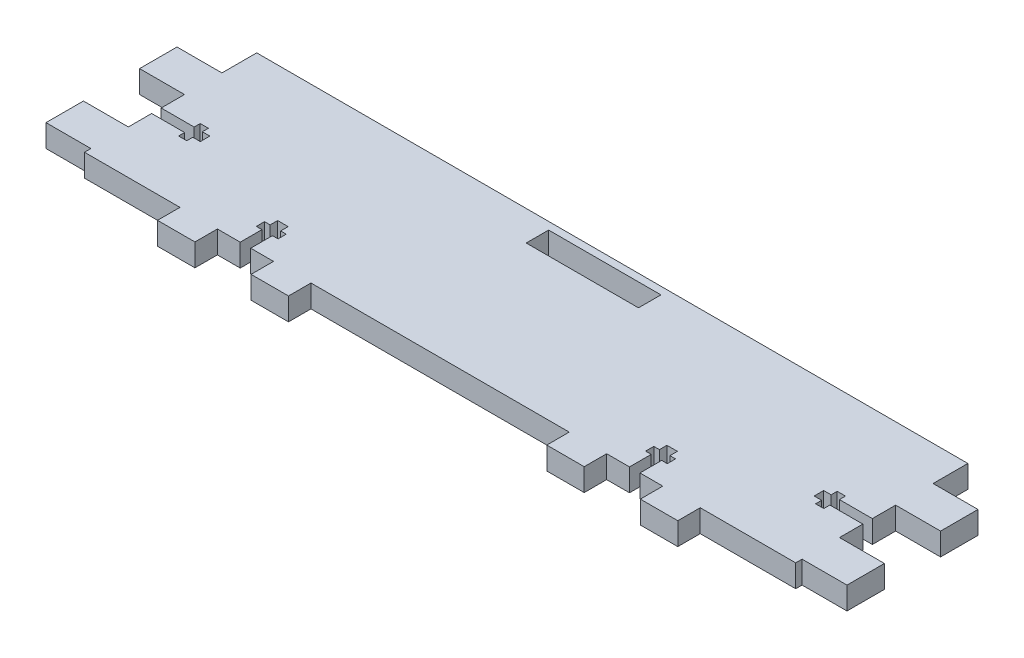
SolidWorks part; units mm, degrees
ref_plane "Front" through (0, 0, 0) normal (0, 0, 1) x (1, 0, 0)
ref_plane "Top" through (0, 0, 0) normal (0, 1, 0) x (1, 0, 0)
ref_plane "Right" through (0, 0, 0) normal (1, 0, 0) x (0, 0, -1)
sketch "Эскиз1" plane through (0, 0, 0) normal (0, 1, 0) x (1, 0, 0)
  line L0 (-131.8881, 0) -> (137.6783, 0) construction
  line L1 (-95, 23) -> (95, 23)
  line L2 (-95, 23) -> (-95, 13.7093)
  line L3 (-95, -23) -> (-69.5, -23)
  line L4 (95, 23) -> (95, 13.7093)
  line L5 (-95, 23) -> (95, -23) construction
  line L6 (-95, -23) -> (95, 23) construction
  line L7 (0, 62.5664) -> (0, -52.5944) construction
  line L8 (69.5, 51.8234) -> (69.5, -44.3584) construction
  line L9 (59.5, 51.8234) -> (59.5, -44.3584) construction
  line L10 (34.5, 51.8234) -> (34.5, -44.3584) construction
  line L11 (44.5, 51.8234) -> (44.5, -44.3584) construction
  line L12 (106.5886, -29) -> (-1.3442, -29) construction
  line L13 (59.5, -23) -> (59.5, -29)
  line L14 (59.5, -29) -> (69.5, -29)
  line L15 (69.5, -29) -> (69.5, -23)
  line L16 (34.5, -23) -> (34.5, -29)
  line L17 (34.5, -29) -> (44.5, -29)
  line L18 (44.5, -29) -> (44.5, -23)
  line L19 (52, -9.9523) -> (52, -35.233) construction
  line L20 (44.5, -23) -> (50.6, -23)
  line L21 (69.5, -23) -> (95, -23)
  line L22 (102.7865, -17.2) -> (39.4134, -17.2) construction
  line L23 (103.2055, -15) -> (39.8324, -15) construction
  line L24 (103.3102, -13) -> (39.9371, -13) construction
  line L25 (50.6, -27.2711) -> (50.6, -9.9523) construction
  line L26 (49.1, -27.2711) -> (49.1, -9.9523) construction
  line L27 (50.6, -23) -> (50.6, -17.2)
  line L28 (50.6, -17.2) -> (49.1, -17.2)
  line L29 (49.1, -17.2) -> (49.1, -15)
  line L30 (49.1, -15) -> (50.6, -15)
  line L31 (50.6, -15) -> (50.6, -13)
  line L32 (50.6, -13) -> (53.4, -13)
  line L33 (53.4, -23) -> (53.4, -17.2)
  line L34 (53.4, -17.2) -> (54.9, -17.2)
  line L35 (54.9, -17.2) -> (54.9, -15)
  line L36 (54.9, -15) -> (53.4, -15)
  line L37 (53.4, -15) -> (53.4, -13)
  line L38 (53.4, -23) -> (59.5, -23)
  line L39 (-50.6, -17.2) -> (-49.1, -17.2)
  line L40 (-49.1, -17.2) -> (-49.1, -15)
  line L41 (-49.1, -15) -> (-50.6, -15)
  line L42 (-50.6, -15) -> (-50.6, -13)
  line L43 (-50.6, -13) -> (-53.4, -13)
  line L44 (-53.4, -15) -> (-53.4, -13)
  line L45 (-54.9, -15) -> (-53.4, -15)
  line L46 (-54.9, -17.2) -> (-54.9, -15)
  line L47 (-53.4, -17.2) -> (-54.9, -17.2)
  line L48 (-53.4, -23) -> (-53.4, -17.2)
  line L49 (-50.6, -23) -> (-50.6, -17.2)
  line L50 (-34.5, -23) -> (-34.5, -29)
  line L51 (-34.5, -29) -> (-44.5, -29)
  line L52 (-44.5, -29) -> (-44.5, -23)
  line L53 (-59.5, -23) -> (-59.5, -29)
  line L54 (-59.5, -29) -> (-69.5, -29)
  line L55 (-69.5, -29) -> (-69.5, -23)
  line L56 (-59.5, -23) -> (-53.4, -23)
  line L57 (-50.6, -23) -> (-44.5, -23)
  line L58 (-34.5, -23) -> (34.5, -23)
  line L59 (107, 23) -> (107, -23) construction
  line L60 (-15, 21) -> (15, 21)
  line L61 (-15, 21) -> (-15, 15)
  line L62 (-15, 15) -> (15, 15)
  line L63 (15, 21) -> (15, 15)
  line L64 (-15, 21) -> (15, 15) construction
  line L65 (-15, 15) -> (15, 21) construction
  line L66 (119.5315, -21.2907) -> (95, -21.2907) construction
  line L67 (95, -21.2907) -> (107, -21.2907)
  line L68 (107, -21.2907) -> (107, -11.2907)
  line L69 (107, -11.2907) -> (95, -11.2907)
  line L70 (119.5315, 3.7093) -> (89.9629, 3.7093) construction
  line L71 (95, 3.7093) -> (107, 3.7093)
  line L72 (107, 3.7093) -> (107, 13.7093)
  line L73 (107, 13.7093) -> (95, 13.7093)
  line L74 (95, 3.7093) -> (95, -2.519)
  line L75 (95, -21.2907) -> (95, -23)
  line L76 (119.5315, -3.7907) -> (75.4928, -3.7907) construction
  line L77 (111.868, -2.519) -> (75.4928, -2.519) construction
  line L78 (111.868, -0.9012) -> (75.4928, -0.9012) construction
  line L79 (82, 3.0697) -> (82, -8.7695) construction
  line L80 (84, 3.0697) -> (84, -8.7695) construction
  line L81 (86.2, 3.0697) -> (86.2, -8.7695) construction
  line L82 (82, -5.0625) -> (82, -2.519)
  line L83 (82, -2.519) -> (84, -2.519)
  line L84 (84, -2.519) -> (84, -0.9012)
  line L85 (84, -0.9012) -> (86.2, -0.9012)
  line L86 (86.2, -0.9012) -> (86.2, -2.519)
  line L87 (86.2, -2.519) -> (95, -2.519)
  line L88 (82, -5.0625) -> (84, -5.0625)
  line L89 (84, -5.0625) -> (84, -6.6803)
  line L90 (84, -6.6803) -> (86.2, -6.6803)
  line L91 (86.2, -6.6803) -> (86.2, -5.0625)
  line L92 (86.2, -5.0625) -> (95, -5.0625)
  line L93 (95, -5.0625) -> (95, -11.2907)
  line L94 (-84, -6.6803) -> (-86.2, -6.6803)
  line L95 (-84, -5.0625) -> (-84, -6.6803)
  line L96 (-82, -5.0625) -> (-84, -5.0625)
  line L97 (-82, -5.0625) -> (-82, -2.519)
  line L98 (-82, -2.519) -> (-84, -2.519)
  line L99 (-84, -2.519) -> (-84, -0.9012)
  line L100 (-84, -0.9012) -> (-86.2, -0.9012)
  line L101 (-86.2, -0.9012) -> (-86.2, -2.519)
  line L102 (-86.2, -6.6803) -> (-86.2, -5.0625)
  line L103 (-86.2, -5.0625) -> (-95, -5.0625)
  line L104 (-86.2, -2.519) -> (-95, -2.519)
  line L105 (-95, -21.2907) -> (-107, -21.2907)
  line L106 (-107, -21.2907) -> (-107, -11.2907)
  line L107 (-107, -11.2907) -> (-95, -11.2907)
  line L108 (-95, 3.7093) -> (-107, 3.7093)
  line L109 (-107, 3.7093) -> (-107, 13.7093)
  line L110 (-107, 13.7093) -> (-95, 13.7093)
  line L111 (-95, 3.7093) -> (-95, -2.519)
  line L112 (-95, -5.0625) -> (-95, -11.2907)
  line L113 (-95, -21.2907) -> (-95, -23)
  point P0 (0, 0)
  point P47 (49.85, -15)
  point P53 (52, -13)
  point P57 (-49.85, -15)
  point P75 (0, 18)
  point P113 (82, -3.7907)
  dimension "D1" = 46
  dimension "D2" = 190
  dimension "D3" = 25.5
  dimension "D4" = 10
  dimension "D5" = 15
  dimension "D6" = 10
  dimension "D7" = 6
  dimension "D8" = 7.5
  dimension "D9" = 10
  dimension "D10" = 2
  dimension "D11" = 2.2
  dimension "D12" = 1.4
  dimension "D13" = 1.5
  dimension "D14" = 6
  dimension "D15" = 30
  dimension "D16" = 2
  dimension "D17" = 12
  dimension "D18" = 10
  dimension "D19" = 15
  dimension "D20" = 10
  dimension "D21" = 7.5
  dimension "D22" = 13
  dimension "D23" = 2
  dimension "D24" = 2.2
extrude "Бобышка-Вытянуть1" add sketch "Эскиз1" along normal blind 6
